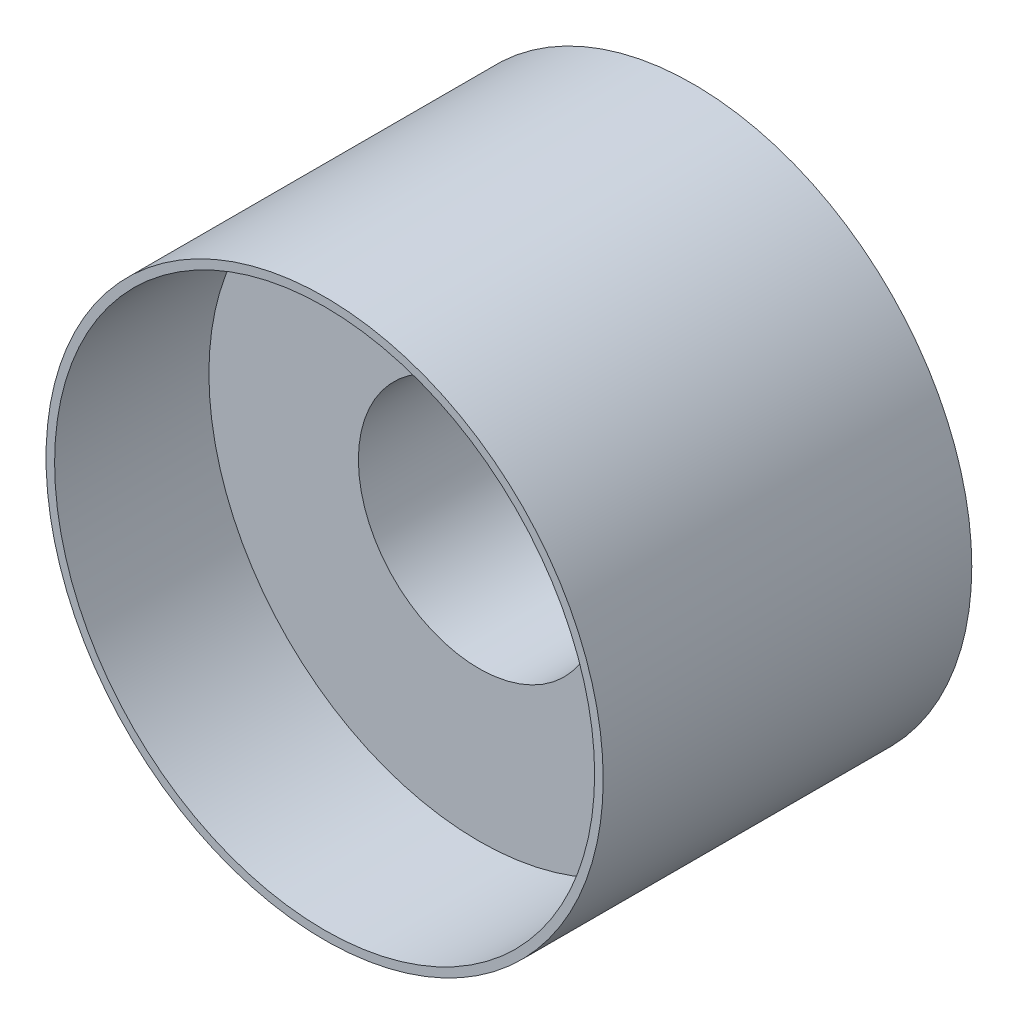
SolidWorks part; units mm, degrees
ref_plane "Front Plane" through (0, 0, 0) normal (0, 0, 1) x (1, 0, 0)
ref_plane "Top Plane" through (0, 0, 0) normal (0, 1, 0) x (1, 0, 0)
ref_plane "Right Plane" through (0, 0, 0) normal (1, 0, 0) x (0, 0, -1)
sketch "Sketch1" plane through (0, 0, 0) normal (0, 0, 1) x (1, 0, 0)
  circle A0 centre (0, 0) radius 6.4008
  circle A1 centre (0, 0) radius 6.604
  dimension "D1" = 12.8016
  dimension "D2" = 13.208
extrude "Boss-Extrude1" add sketch "Sketch1" against normal blind 8.7376
sketch "Sketch2" plane through (0, 0, -8.7376) normal (0, 0, -1) x (-1, 0, 0)
  circle A0 centre (0, 0) radius 6.4008
  circle A1 centre (0, 0) radius 2.8575
  dimension "D1" = 5.715
extrude "Boss-Extrude2" add sketch "Sketch2" against normal blind 5.08
